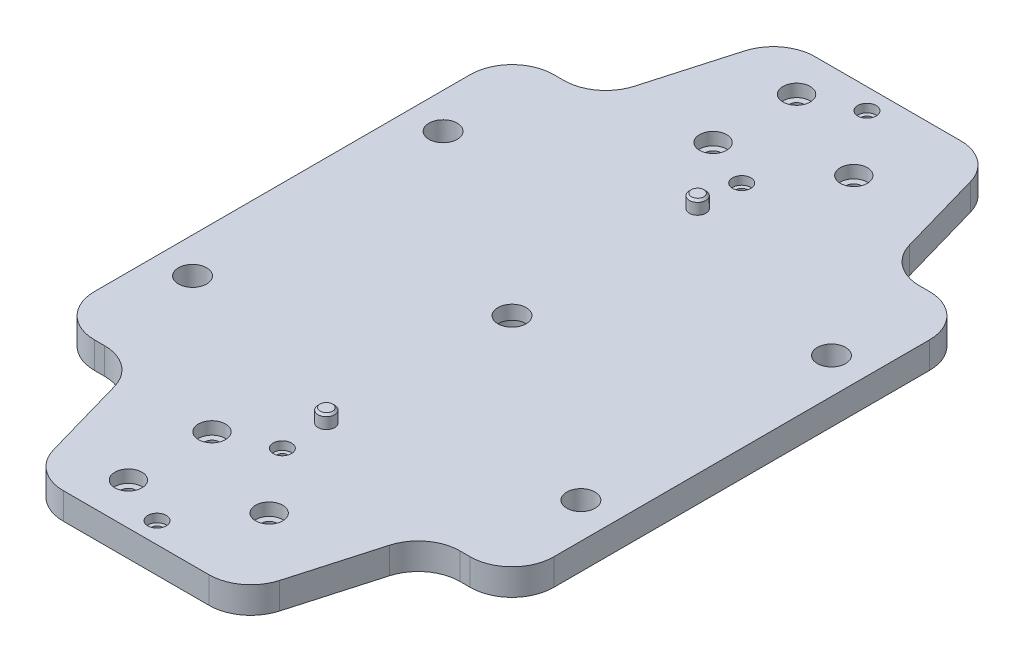
SolidWorks part; units mm, degrees
material "6061 Alloy"
ref_plane "Front Plane" through (0, 0, 0) normal (0, 0, 1) x (1, 0, 0)
ref_plane "Top Plane" through (0, 0, 0) normal (0, 1, 0) x (1, 0, 0)
ref_plane "Right Plane" through (0, 0, 0) normal (1, 0, 0) x (0, 0, -1)
sketch "Sketch1" plane through (0, 0, 0) normal (0, 1, 0) x (1, 0, 0)
  line L0 (35, 55) -> (25, 90)
  line L1 (-55, -55) -> (-35, -55)
  line L2 (-55, -55) -> (-55, 55)
  line L3 (-55, 55) -> (-35, 55)
  line L4 (55, -55) -> (55, 55)
  line L5 (-55, -55) -> (55, 55) construction
  line L6 (-55, 55) -> (55, -55) construction
  line L7 (25, 90) -> (-25, 90)
  line L8 (-25, 90) -> (-35, 55)
  line L9 (55, 0) -> (-55, 0) construction
  line L10 (-11.85, 80) -> (-11.85, 60) construction
  line L11 (11.85, 70) -> (-11.85, 70) construction
  line L12 (0, 55) -> (0, 85) construction
  line L13 (0, -55) -> (0, -85) construction
  line L14 (11.85, -70) -> (-11.85, -70) construction
  line L15 (-11.85, -80) -> (-11.85, -60) construction
  line L16 (-25, -90) -> (-35, -55)
  line L17 (25, -90) -> (-25, -90)
  line L18 (35, -55) -> (25, -90)
  line L19 (-35, -55) -> (35, -55) construction
  line L20 (35, -55) -> (55, -55)
  line L21 (-35, 55) -> (35, 55) construction
  line L22 (35, 55) -> (55, 55)
  line L23 (0, 55) -> (0, -55) construction
  point P0 (0, 0)
  point P14 (0, 90)
  point P15 (-11.85, 80)
  point P18 (-11.85, 60)
  point P24 (0, 85)
  point P27 (0, 70)
  point P28 (0, 55)
  point P30 (0, 70)
  point P48 (11.85, -70)
  point P49 (11.85, 70)
  point P50 (0, -55)
  point P51 (0, -85)
  point P52 (-11.85, -60)
  point P53 (-11.85, -80)
  dimension "D2" = 110
  dimension "D1" = 110
  dimension "D3" = 35
  dimension "D4" = 10
  dimension "D5" = 50
  dimension "D6" = 20
  dimension "D7" = 23.7
  dimension "D8" = 30
extrude "Boss-Extrude1" add sketch "Sketch1" along normal blind 6.35
hole_wizard "CBORE for 1/4 Socket Head Cap Screw1" positions "Sketch2" profile "Sketch4" counterbore size "1/4" standard "ANSI Inch" end condition through all
sketch "Sketch2" plane through (0, 0, 0) normal (0, -1, 0) x (-1, 0, 0)
  point P0 (0, 0)
sketch "Sketch4" plane through (0, 0, 0) normal (1, 0, 0) x (0, 0, -1)
  line L0 (0, 0) -> (0, 6.35)
  line L1 (0, 6.35) -> (3.3782, 6.35)
  line L3 (3.3782, 6.35) -> (3.3782, 3)
  line L4 (3.3782, 3) -> (5.5562, 3)
  line L5 (5.5562, 3) -> (5.5562, 0)
  line L7 (5.5562, 0) -> (0, 0)
  line L11 (0, -6.35) -> (0, 107.95) construction
  dimension "Thru Hole Dia." = 6.7564
  dimension "Thru Hole Depth" = 6.35
  dimension "C'Bore Dia." = 11.1125
  dimension "C'Bore Depth" = 3
hole_wizard "1/8 (0.15625) Press Dowel Hole1" positions "Sketch7" profile "Sketch8" hole size "1/8" standard "ANSI Inch" end condition through all
sketch "Sketch7" plane through (0, 6.35, 0) normal (0, 1, 0) x (1, 0, 0)
  line L0 (0, -44.45) -> (0, 44.45) construction
  point P0 (0, 44.45)
  point P2 (0, -44.45)
  point P20 (0, 0)
  point P21 (0, 0)
  point P22 (0, 0)
  point P23 (-3.2403, -44.3317)
  dimension "D1" = 88.9
sketch "Sketch8" plane through (0, 6.35, -44.45) normal (1, 0, 0) x (0, 0, 1)
  line L0 (0, 0) -> (0, 6.35)
  line L1 (0, 6.35) -> (1.9844, 6.35)
  line L2 (1.9844, 6.35) -> (1.9844, 0)
  line L5 (1.9844, 0) -> (0, 0)
  line L11 (0, -6.35) -> (0, 107.95) construction
  dimension "Thru Hole Dia." = 3.9688
  dimension "Thru Hole Depth" = 6.35
sketch "Sketch13" plane through (0, 0, 0) normal (0, 1, 0) x (1, 0, 0)
  circle A0 centre (0, -44.45) radius 1.9844
  circle A1 centre (0, 44.45) radius 1.9844
  dimension "D1" = 3.9688
extrude "Boss-Extrude4" add sketch "Sketch13" along normal blind 9.525 separate body
chamfer "Chamfer1" distance 0.5 angle 45 2 edges at (0, 0, 46.4344) (0, 9.525, 46.4344)
chamfer "Chamfer2" distance 0.5 angle 45 2 edges at (0, 0, -42.4656) (0, 9.525, -42.4656)
sketch "Sketch14" plane through (0, 0, 0) normal (0, -1, 0) x (-1, 0, 0)
  point P0 (46.5, 30)
  point P1 (46.5, -30)
  point P3 (-46.5, -30)
  point P5 (-46.5, 30)
hole_wizard "1/4 Clearance Hole1" positions "Sketch15" profile "Sketch16" hole size "1/4" standard "ANSI Inch" end condition up to next
sketch "Sketch15" plane through (0, 0, 0) normal (0, -1, 0) x (-1, 0, 0)
  point P0 (46.5, 30)
  point P3 (46.5, -30)
  point P6 (-46.5, -30)
  point P9 (-46.5, 30)
sketch "Sketch16" plane through (-46.5, 0, -30) normal (1, 0, 0) x (0, 0, -1)
  line L0 (0, 0) -> (0, 6.35)
  line L1 (0, 6.35) -> (3.3782, 6.35)
  line L2 (3.3782, 6.35) -> (3.3782, 0)
  line L5 (3.3782, 0) -> (0, 0)
  line L11 (0, -6.35) -> (0, 107.95) construction
  dimension "Thru Hole Dia." = 6.7564
  dimension "Thru Hole Depth" = 6.35
hole_wizard "CBORE for M2 SHCS2" positions "Sketch21" profile "Sketch22" counterbore size "M2" standard "ANSI Metric" end condition through all
sketch "Sketch21" plane through (0, 6.35, 0) normal (0, 1, 0) x (1, 0, 0)
  line L0 (0, 0) -> (49.5174, 0) construction
  point P0 (0, 85)
  point P2 (0, 55)
  point P16 (0, -85)
  point P17 (0, -55)
sketch "Sketch22" plane through (0, 6.35, -85) normal (1, 0, 0) x (0, 0, 1)
  line L0 (0, 0) -> (0, 6.35)
  line L1 (0, 6.35) -> (1.3, 6.35)
  line L3 (1.3, 6.35) -> (1.3, 2)
  line L4 (1.3, 2) -> (2.2, 2)
  line L5 (2.2, 2) -> (2.2, 0)
  line L7 (2.2, 0) -> (0, 0)
  line L11 (0, -6.35) -> (0, 107.95) construction
  dimension "Thru Hole Dia." = 2.6
  dimension "Thru Hole Depth" = 6.35
  dimension "C'Bore Dia." = 4.4
  dimension "C'Bore Depth" = 2
hole_wizard "CBORE for M3 SHCS2" positions "Sketch23" profile "Sketch24" counterbore size "M3" standard "ANSI Metric" end condition through all
sketch "Sketch23" plane through (0, 6.35, 0) normal (0, 1, 0) x (1, 0, 0)
  point P0 (-11.85, 80)
  point P2 (-11.85, 60)
  point P4 (11.85, 70)
  point P14 (-11.85, -80)
  point P16 (11.85, -70)
  point P18 (-11.85, -60)
sketch "Sketch24" plane through (-11.85, 6.35, -80) normal (1, 0, 0) x (0, 0, 1)
  line L0 (0, 0) -> (0, 6.35)
  line L1 (0, 6.35) -> (1.8, 6.35)
  line L3 (1.8, 6.35) -> (1.8, 3)
  line L4 (1.8, 3) -> (3.25, 3)
  line L5 (3.25, 3) -> (3.25, 0)
  line L7 (3.25, 0) -> (0, 0)
  line L11 (0, -6.35) -> (0, 107.95) construction
  dimension "Thru Hole Dia." = 3.6
  dimension "Thru Hole Depth" = 6.35
  dimension "C'Bore Dia." = 6.5
  dimension "C'Bore Depth" = 3
fillet "Fillet1" radius 10 12 edges at (25, 3.175, 90) (-25, 3.175, 90) (-35, 3.175, 55) (-55, 3.175, 55) (-55, 3.175, -55) (-35, 3.175, -55) (-25, 3.175, -90) (25, 3.175, -90) (35, 3.175, -55) (35, 3.175, 55) (55, 3.175, 55) (55, 3.175, -55)
equation "\"D5@Sketch1\"=50"
